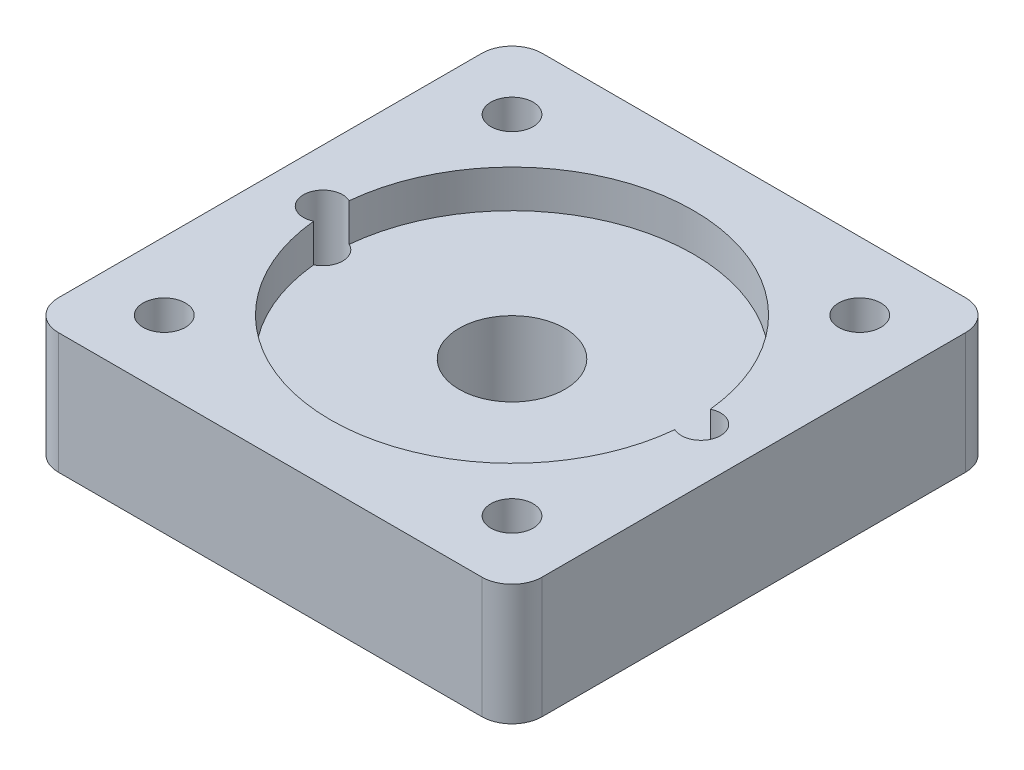
SolidWorks part; units mm, degrees
material "ABS"
ref_plane "Front Plane" through (0, 0, 0) normal (0, 0, 1) x (1, 0, 0)
ref_plane "Top Plane" through (0, 0, 0) normal (0, 1, 0) x (1, 0, 0)
ref_plane "Right Plane" through (0, 0, 0) normal (1, 0, 0) x (0, 0, -1)
sketch "Sketch1" plane through (0, 0, 0) normal (0, 1, 0) x (1, 0, 0)
  line L0 (0, 16) -> (32, 16) construction
  line L1 (0, 0) -> (32, 0)
  line L2 (0, 0) -> (0, 32)
  line L3 (0, 32) -> (32, 32)
  line L4 (32, 0) -> (32, 32)
  line L5 (16, 32) -> (16, 0) construction
  circle A0 centre (3.5, 16) radius 1.3
  circle A1 centre (4.5, 27.5) radius 1.4
  circle A2 centre (27.5, 27.5) radius 1.4
  circle A3 centre (27.5, 4.5) radius 1.4
  circle A4 centre (4.5, 4.5) radius 1.4
  circle A5 centre (28.5, 16) radius 1.3
  circle A7 centre (16, 16) radius 3.5
  dimension "D2" = 2.6
  dimension "D3" = 25
  dimension "D4" = 23
  dimension "D5" = 23
  dimension "D6" = 2.8
  dimension "D7" = 7
  dimension "D1" = 32
extrude "Boss-Extrude1" add sketch "Sketch1" along normal blind 8
sketch "Sketch2" plane through (0, 8, 0) normal (0, 1, 0) x (1, 0, 0)
  line L0 (16, 32) -> (16, 0) construction
  line L1 (32, 32) -> (0, 32) construction
  line L2 (0, 0) -> (32, 0) construction
  circle A0 centre (16, 16) radius 12
  dimension "D1" = 24
extrude "Cut-Extrude1" cut sketch "Sketch2" against normal blind 2.5
fillet "Fillet1" radius 2 4 edges at (32, 4, -32) (32, 4, 0) (0, 4, 0) (0, 4, -32)
sketch "Sketch3" plane through (0, 0, 0) normal (0, -1, 0) x (1, 0, 0)
  circle A0 centre (27.5, -4.5) radius 3
  circle A1 centre (27.5, -27.5) radius 3
  circle A2 centre (4.5, -27.5) radius 3
  circle A3 centre (4.5, -4.5) radius 3
  dimension "D1" = 6
extrude "Cut-Extrude2" cut sketch "Sketch3" against normal blind 3
